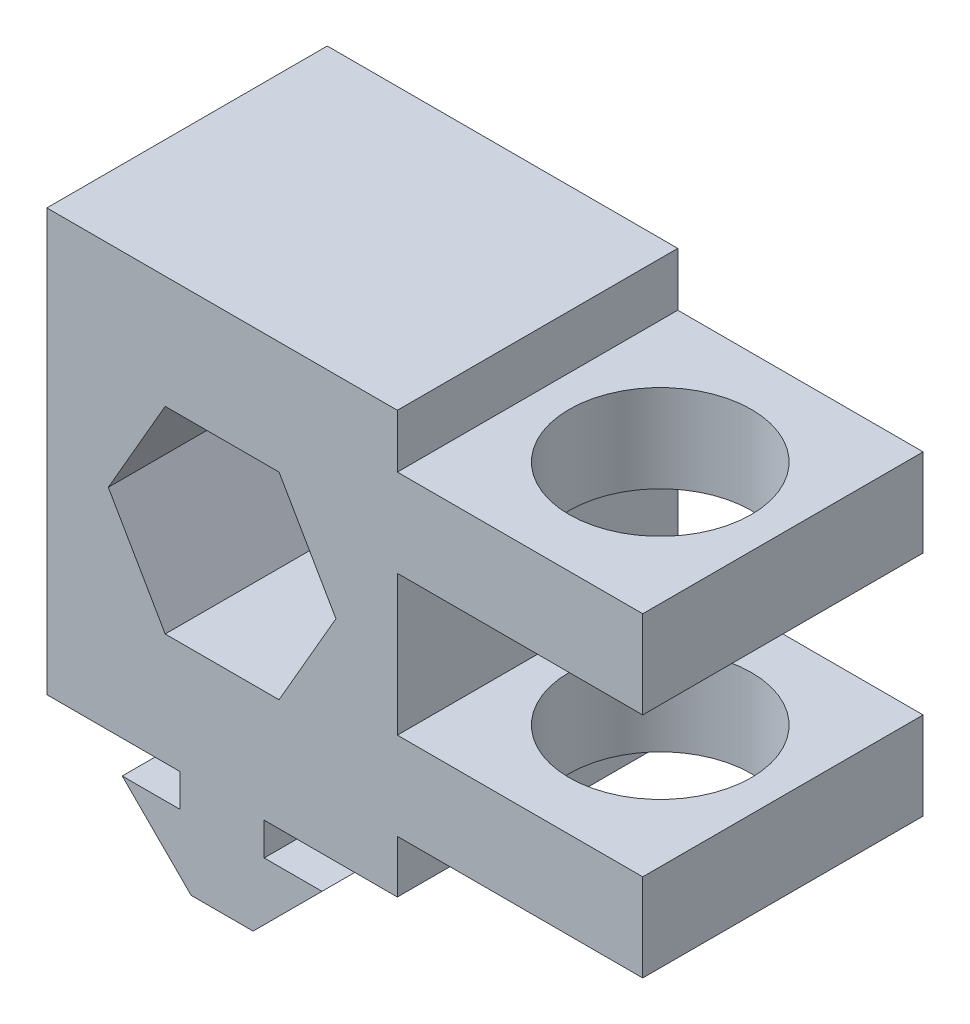
SolidWorks part; units mm, degrees
ref_plane "Front Plane" through (0, 0, 0) normal (0, 0, 1) x (1, 0, 0)
ref_plane "Top Plane" through (0, 0, 0) normal (0, 1, 0) x (1, 0, 0)
ref_plane "Right Plane" through (0, 0, 0) normal (1, 0, 0) x (0, 0, -1)
sketch "Sketch1" plane through (0, 0, 0) normal (0, 0, 1) x (1, 0, 0)
  line L0 (0, 42.8899) -> (0, -3.5389) construction
  line L1 (2.2454, 0) -> (-2.2454, 0)
  line L2 (-2.2454, 0) -> (-7.239, 4.9936)
  line L3 (-7.239, 4.9936) -> (-3.048, 4.9936)
  line L4 (-3.048, 4.9936) -> (-3.048, 7.366)
  line L5 (-3.048, 7.366) -> (-12.7, 7.366)
  line L6 (-4.1244, 29.7498) -> (-8.2489, 22.606)
  line L7 (-8.2489, 22.606) -> (-4.1244, 15.4622)
  line L8 (-4.1244, 15.4622) -> (4.1244, 15.4622)
  line L9 (4.1244, 15.4622) -> (8.2489, 22.606)
  line L10 (8.2489, 22.606) -> (4.1244, 29.7497)
  line L11 (4.1244, 29.7497) -> (-4.1244, 29.7498)
  line L12 (-12.7, 7.366) -> (-12.7, 37.9166)
  line L13 (-12.7, 37.9166) -> (12.7, 37.9166)
  line L14 (2.2454, 0) -> (7.239, 4.9936)
  line L15 (7.239, 4.9936) -> (3.048, 4.9936)
  line L16 (3.048, 4.9936) -> (3.048, 7.366)
  line L17 (3.048, 7.366) -> (12.7, 7.366)
  line L18 (12.7, 7.366) -> (12.7, 11.176)
  line L19 (12.7, 34.036) -> (30.48, 34.036)
  line L20 (30.48, 34.036) -> (30.48, 27.686)
  line L21 (30.48, 27.686) -> (12.7, 27.686)
  line L22 (12.7, 17.526) -> (30.48, 17.526)
  line L23 (30.48, 17.526) -> (30.48, 11.176)
  line L24 (30.48, 11.176) -> (12.7, 11.176)
  line L25 (32.9386, 22.606) -> (-19.7176, 22.606) construction
  line L26 (12.7, 34.036) -> (12.7, 37.9166)
  line L27 (12.7, 17.526) -> (12.7, 27.686)
  circle A0 centre (0, 22.606) radius 7.1437 construction
  point P22 (0, 0)
  point P28 (0, 37.9166)
  dimension "D1" = 6.096
  dimension "D2" = 7.366
  dimension "D3" = 45
  dimension "D4" = 14.478
  dimension "D5" = 2.3724
  dimension "D6" = 14.2875
  dimension "D7" = 15.24
  dimension "D8" = 8.1668
  dimension "D9" = 25.4
  dimension "D10" = 5.08
  dimension "D11" = 6.35
  dimension "D12" = 17.78
  dimension "D13" = 5.08
extrude "Boss-Extrude1" add sketch "Sketch1" along normal mid plane 20.32
sketch "Sketch2" plane through (0, 37.9166, 0) normal (0, 1, 0) x (1, 0, 0)
  line L0 (30.48, -10.16) -> (12.7, -10.16) construction
  line L1 (30.48, -10.16) -> (12.7, -10.16) construction
  circle A0 centre (21.59, 0) radius 6.604
  point P5 (21.59, -10.16)
  dimension "D1" = 13.208
extrude "Cut-Extrude1" cut sketch "Sketch2" against normal through all
